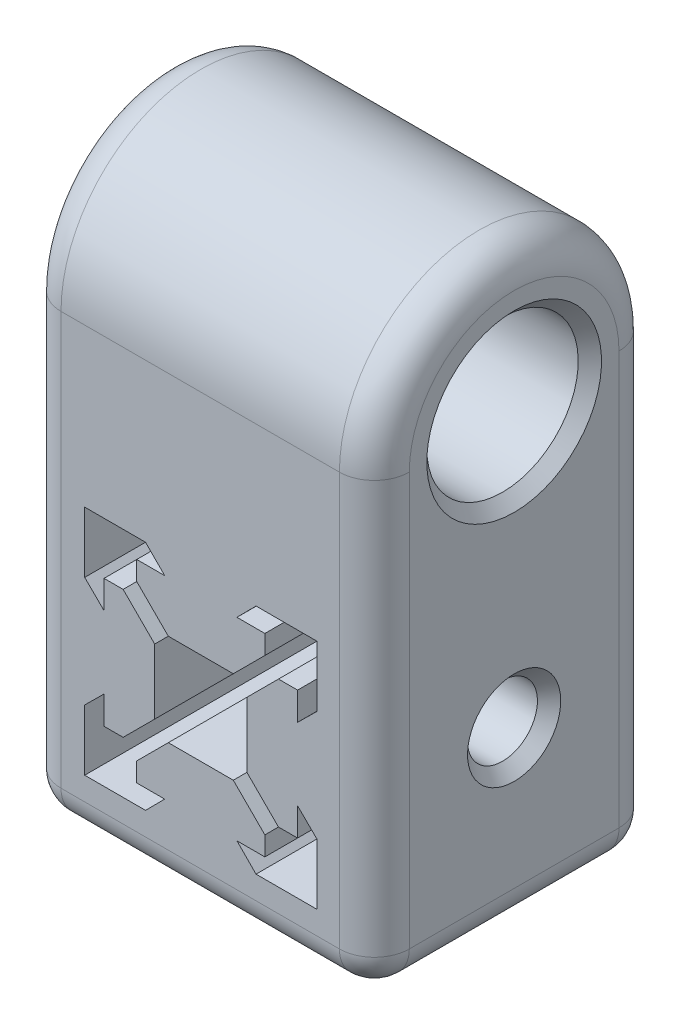
SolidWorks part; units mm, degrees
ref_plane "Front Plane" through (0, 0, 0) normal (0, 0, 1) x (1, 0, 0)
ref_plane "Top Plane" through (0, 0, 0) normal (0, 1, 0) x (1, 0, 0)
ref_plane "Right Plane" through (0, 0, 0) normal (1, 0, 0) x (0, 0, -1)
sketch "Sketch1" plane through (0, 0, 0) normal (0, 0, 1) x (1, 0, 0)
  line L0 (0, -15) -> (0, 15) construction
  line L1 (0, 15) -> (14.8993, 15)
  line L2 (14.8993, 15) -> (14.8993, -14.9496)
  line L3 (14.8993, -14.9496) -> (-15, -14.9496)
  line L4 (-15, -14.9496) -> (-15, 15)
  line L5 (-15, 15) -> (0, 15)
  line L6 (0, -9.9664) -> (0, 9.9664) construction
  line L7 (0, 9.9664) -> (-9.9664, 9.9664) construction
  line L8 (-9.9664, 9.9664) -> (-4.7414, 9.9664)
  line L9 (-4.7414, 9.9664) -> (-3.1, 8.3075)
  line L10 (-3.1, 8.3075) -> (0, 8.3075) construction
  line L11 (-3.1, 8.3075) -> (-5.5, 8.3075)
  line L12 (-5.5, 8.3075) -> (-5.5, 6.6675)
  line L13 (-5.5, 6.6675) -> (-2.79, 3.9575)
  line L14 (-2.79, 3.9575) -> (0, 3.9575) construction
  line L15 (-2.79, 3.9575) -> (2.79, 3.9575)
  line L16 (-9.9664, 9.9664) -> (0, 0) construction
  line L17 (-3.9575, 2.79) -> (-3.9575, -2.79)
  line L18 (-6.6675, 5.5) -> (-3.9575, 2.79)
  line L19 (-8.3075, 5.5) -> (-6.6675, 5.5)
  line L20 (-8.3075, 3.1) -> (-8.3075, 5.5)
  line L21 (-9.9664, 4.7414) -> (-8.3075, 3.1)
  line L22 (-9.9664, 9.9664) -> (-9.9664, 4.7414)
  line L23 (0, 0) -> (-11.0308, 0) construction
  line L24 (5.5, 6.6675) -> (2.79, 3.9575)
  line L25 (5.5, 8.3075) -> (5.5, 6.6675)
  line L26 (3.1, 8.3075) -> (5.5, 8.3075)
  line L27 (4.7414, 9.9664) -> (3.1, 8.3075)
  line L28 (9.9664, 9.9664) -> (4.7414, 9.9664)
  line L29 (9.9664, 9.9664) -> (9.9664, 4.7414)
  line L30 (9.9664, 4.7414) -> (8.3075, 3.1)
  line L31 (8.3075, 3.1) -> (8.3075, 5.5)
  line L32 (8.3075, 5.5) -> (6.6675, 5.5)
  line L33 (6.6675, 5.5) -> (3.9575, 2.79)
  line L34 (3.9575, 2.79) -> (3.9575, -2.79)
  line L35 (-9.9664, -9.9664) -> (0, 0) construction
  line L36 (-2.79, -3.9575) -> (0, -3.9575) construction
  line L37 (-3.1, -8.3075) -> (0, -8.3075) construction
  line L38 (0, -9.9664) -> (-9.9664, -9.9664) construction
  line L39 (6.6675, -5.5) -> (3.9575, -2.79)
  line L40 (8.3075, -5.5) -> (6.6675, -5.5)
  line L41 (8.3075, -3.1) -> (8.3075, -5.5)
  line L42 (9.9664, -4.7414) -> (8.3075, -3.1)
  line L43 (9.9664, -9.9664) -> (9.9664, -4.7414)
  line L44 (9.9664, -9.9664) -> (4.7414, -9.9664)
  line L45 (4.7414, -9.9664) -> (3.1, -8.3075)
  line L46 (3.1, -8.3075) -> (5.5, -8.3075)
  line L47 (5.5, -8.3075) -> (5.5, -6.6675)
  line L48 (5.5, -6.6675) -> (2.79, -3.9575)
  line L49 (-9.9664, -9.9664) -> (-9.9664, -4.7414)
  line L50 (-9.9664, -4.7414) -> (-8.3075, -3.1)
  line L51 (-8.3075, -3.1) -> (-8.3075, -5.5)
  line L52 (-8.3075, -5.5) -> (-6.6675, -5.5)
  line L53 (-6.6675, -5.5) -> (-3.9575, -2.79)
  line L54 (-2.79, -3.9575) -> (2.79, -3.9575)
  line L55 (-5.5, -6.6675) -> (-2.79, -3.9575)
  line L56 (-5.5, -8.3075) -> (-5.5, -6.6675)
  line L57 (-3.1, -8.3075) -> (-5.5, -8.3075)
  line L58 (-4.7414, -9.9664) -> (-3.1, -8.3075)
  line L59 (-9.9664, -9.9664) -> (-4.7414, -9.9664)
  point P43 (3.9575, 0)
  point P58 (-3.9575, 0)
  dimension "D1" = 3.1
  dimension "D2" = 2.79
  dimension "D3" = 2.4
  dimension "D4" = 135
  dimension "D5" = 1.64
  dimension "D6" = 15
  dimension "D7" = 15
  dimension "D8" = 9.9664
  dimension "D9" = 5.225
extrude "Boss-Extrude1" add sketch "Sketch1" along normal blind 24
sketch "Sketch5" plane through (-15, 0, 0) normal (-1, 0, 0) x (0, 0, 1)
  line L2 (0, 15) -> (24, 15)
  line L10 (0, 23.5) -> (0, 15)
  line L11 (12, 17) -> (12, 23.5) construction
  line L13 (24, 23.5) -> (24, 15)
  circle A2 centre (12, 23.5) radius 6.5
  arc A3 (0, 23.5) -> (24, 23.5) centre (12, 23.5) cw
  dimension "D3" = 13
  dimension "D5" = 6.5
  dimension "D4" = 2
  dimension "D6" = 12
extrude "Boss-Extrude3" add sketch "Sketch5" against normal through all
sketch "Sketch3" plane through (-15, 0, 0) normal (-1, 0, 0) x (0, 0, 1)
  line L0 (12, 0) -> (24, 4.2752) construction
  line L2 (0, 0) -> (12, 0) construction
  line L3 (24, 23.5) -> (24, -14.9496) construction
  circle A0 centre (12, 0) radius 3
extrude "Cut-Extrude1" cut sketch "Sketch3" against normal through all
fillet "Fillet1" radius 3 10 edges at (-0.0504, -14.9496, 24) (14.8993, 4.2752, 24) (-15, 4.2752, 24) (14.8993, 4.2752, 0) (-15, 4.2752, 0) (-0.0504, -14.9496, 0) (14.8993, -14.9496, 12) (-15, -14.9496, 12) (-15, 35.5, 12) (14.8993, 35.5, 12)
chamfer "Chamfer1" distance 1 angle 45 4 edges at (-15, 0, 15) (-15, 23.5, 18.5) (14.8993, 0, 15) (14.8993, 23.5, 18.5)
